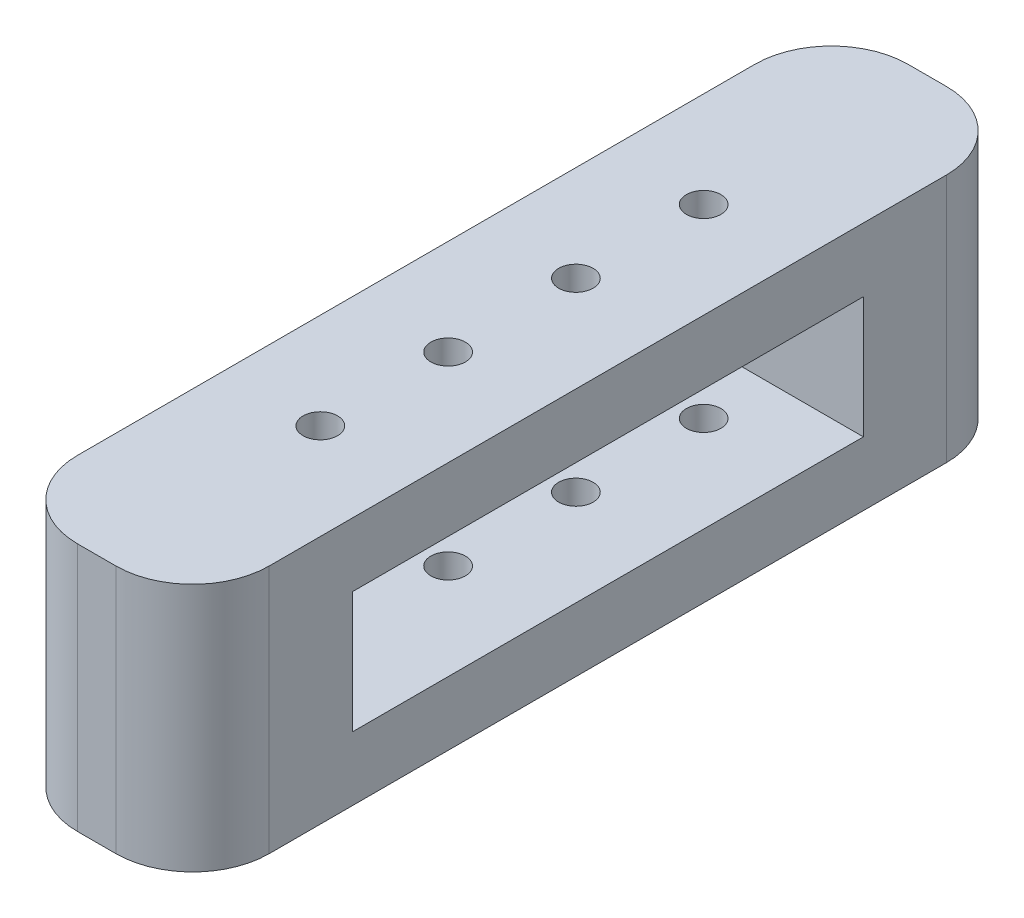
SolidWorks part; units mm, degrees
ref_plane "Front Plane" through (0, 0, 0) normal (0, 0, 1) x (1, 0, 0)
ref_plane "Top Plane" through (0, 0, 0) normal (0, 1, 0) x (1, 0, 0)
ref_plane "Right Plane" through (0, 0, 0) normal (1, 0, 0) x (0, 0, -1)
sketch "Sketch1" plane through (0, 0, 0) normal (0, 1, 0) x (1, 0, 0)
  line L0 (0, 0) -> (0, -65) construction
  line L1 (-7.5, 0) -> (7.5, 0)
  line L2 (-7.5, 0) -> (-7.5, -65)
  line L3 (-7.5, -65) -> (7.5, -65)
  line L4 (7.5, 0) -> (7.5, -65)
  circle A1 centre (0, -17.5) radius 1.35
  circle A2 centre (0, -27.5) radius 1.35
  circle A3 centre (0, -37.5) radius 1.35
  circle A6 centre (0, -47.5) radius 1.35
  dimension "D3" = 17.5
  dimension "D5" = 2.7
  dimension "D6" = 10
  dimension "D7" = 10
  dimension "D9" = 10
  dimension "D1" = 15
  dimension "D2" = 65
extrude "Boss-Extrude1" add sketch "Sketch1" along normal blind 19.5
fillet "Fillet1" radius 6 4 edges at (-7.5, 9.75, 65) (7.5, 9.75, 65) (-7.5, 9.75, 0) (7.5, 9.75, 0)
sketch "Sketch2" plane through (-7.5, 0, 0) normal (-1, 0, 0) x (0, 0, 1)
  line L0 (32.5, 19.5) -> (32.5, 0) construction
  line L1 (12.5, 14.5) -> (52.5, 14.5)
  line L2 (12.5, 14.5) -> (12.5, 5)
  line L3 (12.5, 5) -> (52.5, 5)
  line L4 (52.5, 14.5) -> (52.5, 5)
  line L5 (12.5, 14.5) -> (52.5, 5) construction
  line L6 (12.5, 5) -> (52.5, 14.5) construction
  line L7 (6, 19.5) -> (59, 19.5) construction
  line L8 (6, 0) -> (59, 0) construction
  point P0 (32.5, 9.75)
  dimension "D1" = 40
  dimension "D2" = 5
extrude "Cut-Extrude1" cut sketch "Sketch2" against normal blind 20
